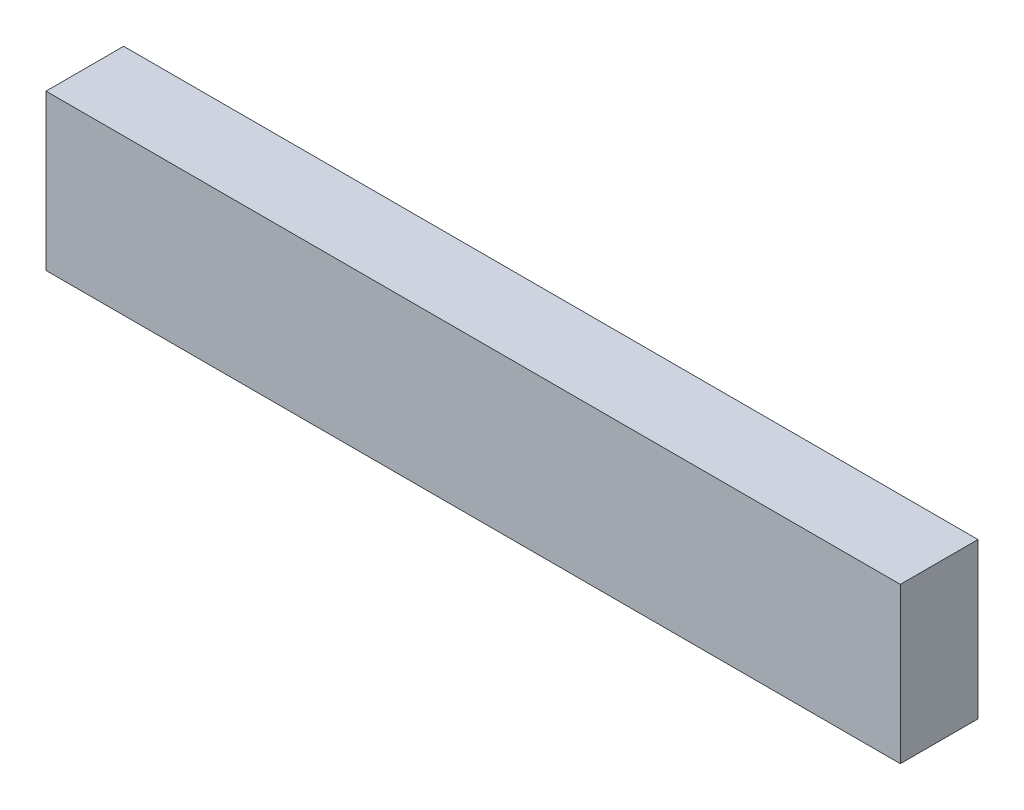
SolidWorks part; units mm, degrees
ref_plane "Спереди" through (0, 0, 0) normal (0, 0, 1) x (1, 0, 0)
ref_plane "Сверху" through (0, 0, 0) normal (0, 1, 0) x (1, 0, 0)
ref_plane "Справа" through (0, 0, 0) normal (1, 0, 0) x (0, 0, -1)
sketch "Эскиз1" plane through (0, 0, 0) normal (1, 0, 0) x (0, 0, -1)
  line L1 (0, 0) -> (20, 0)
  line L2 (0, 0) -> (0, 40)
  line L3 (0, 40) -> (20, 40)
  line L4 (20, 0) -> (20, 40)
extrude "Бобышка-Вытянуть1" add sketch "Эскиз1" along normal blind 220
